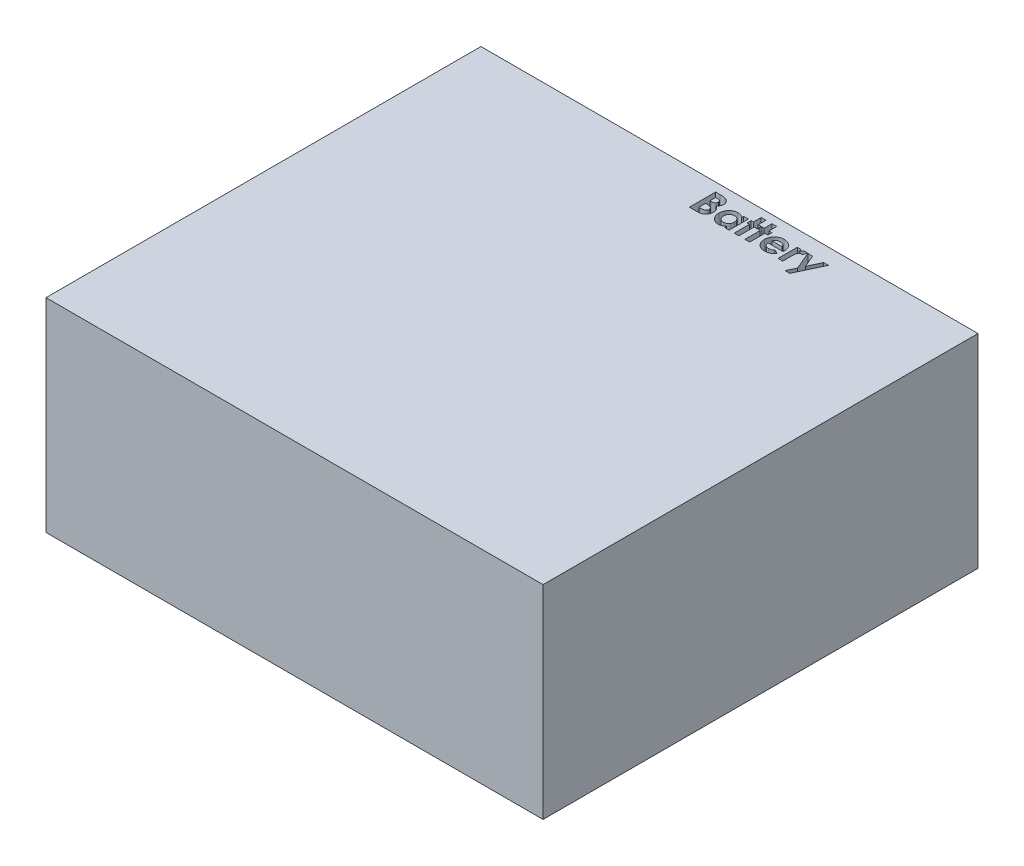
SolidWorks part; units mm, degrees
ref_plane "Front Plane" through (0, 0, 0) normal (0, 0, 1) x (1, 0, 0)
ref_plane "Top Plane" through (0, 0, 0) normal (0, 1, 0) x (1, 0, 0)
ref_plane "Right Plane" through (0, 0, 0) normal (1, 0, 0) x (0, 0, -1)
sketch "Sketch1" plane through (0, 0, 0) normal (0, 1, 0) x (1, 0, 0)
  line L1 (0, 0) -> (240, 0)
  line L2 (0, 0) -> (0, 210)
  line L3 (0, 210) -> (240, 210)
  line L4 (240, 0) -> (240, 210)
  dimension "D1" = 210
  dimension "D2" = 240
extrude "Boss-Extrude1" add sketch "Sketch1" along normal blind 98.2
sketch "Sketch2" plane through (0, 98.2, 0) normal (0, 1, 0) x (1, 0, 0)
  line L0 (67.2536, 193.1336) -> (224.5641, 193.1336) construction
  text T0 "<b>Battery</b>" font "Century Gothic" height in points 48
extrude "Cut-Extrude1" cut sketch "Sketch2" against normal blind 101.6
